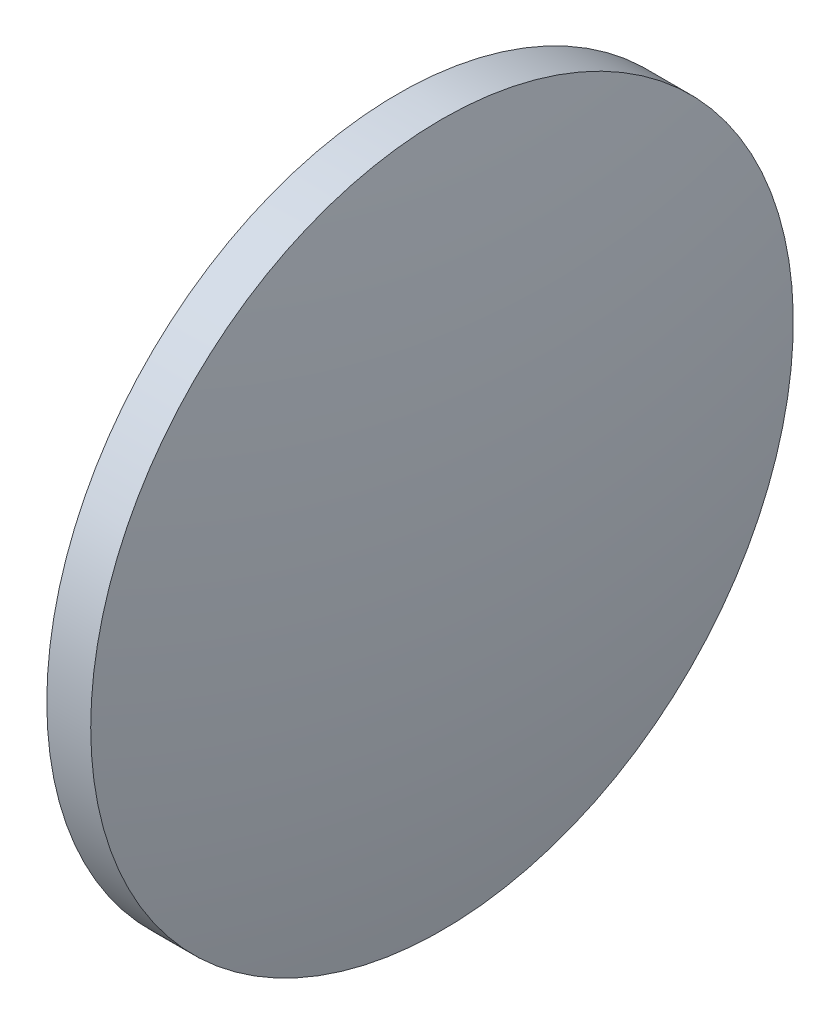
SolidWorks part; units mm, degrees
ref_plane "前视基准面" through (0, 0, 0) normal (0, 0, 1) x (1, 0, 0)
ref_plane "上视基准面" through (0, 0, 0) normal (0, 1, 0) x (1, 0, 0)
ref_plane "右视基准面" through (0, 0, 0) normal (1, 0, 0) x (0, 0, -1)
sketch "草图1" plane through (0, 0, 0) normal (0, 0, 1) x (1, 0, 0)
  line L0 (764.1774, 193.8494) -> (783.3536, 193.8494) construction
  line L1 (768.872, 193.8494) -> (768.872, 213.8494)
  line L2 (773.322, 193.8494) -> (768.872, 193.8494)
  line L5 (768.872, 213.8494) -> (771.372, 213.8494)
  arc A0 (773.322, 193.8494) -> (771.372, 213.8494) centre (669.7829, 193.8494) ccw
revolve "旋转1" add sketch "草图1" angle 360 about L0
